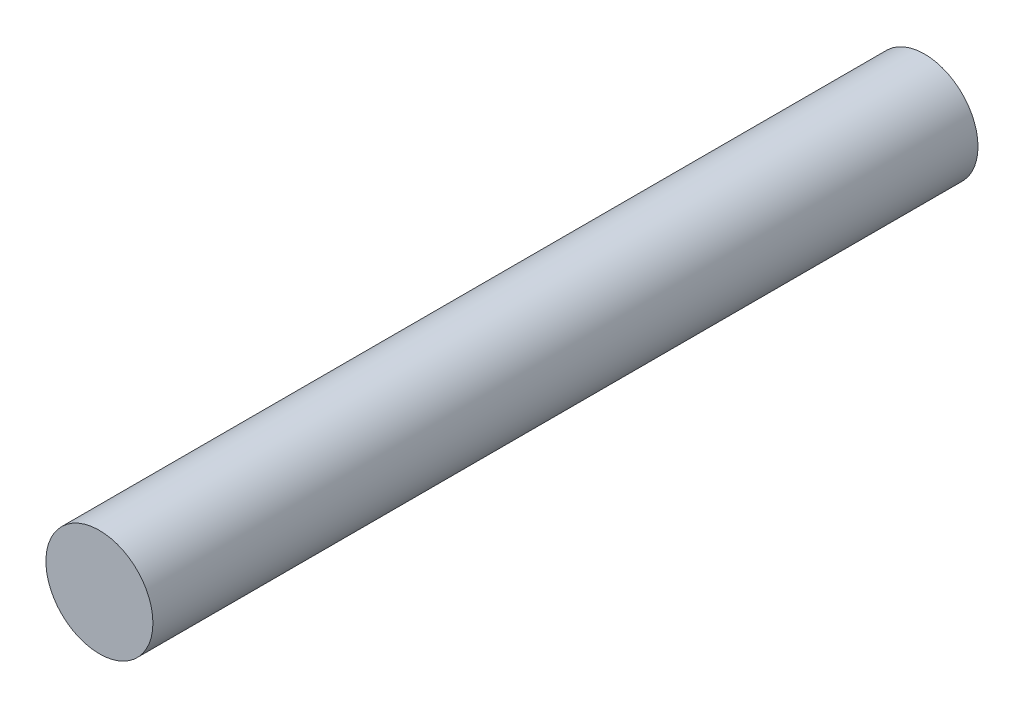
SolidWorks part; units mm, degrees
ref_plane "Front Plane" through (0, 0, 0) normal (0, 0, 1) x (1, 0, 0)
ref_plane "Top Plane" through (0, 0, 0) normal (0, 1, 0) x (1, 0, 0)
ref_plane "Right Plane" through (0, 0, 0) normal (1, 0, 0) x (0, 0, -1)
sketch "Sketch1" plane through (0, 0, 0) normal (0, 0, 1) x (1, 0, 0)
  circle A0 centre (0, 0) radius 2.8
  dimension "D1" = 5.6
extrude "Boss-Extrude1" add sketch "Sketch1" along normal blind 43.18
